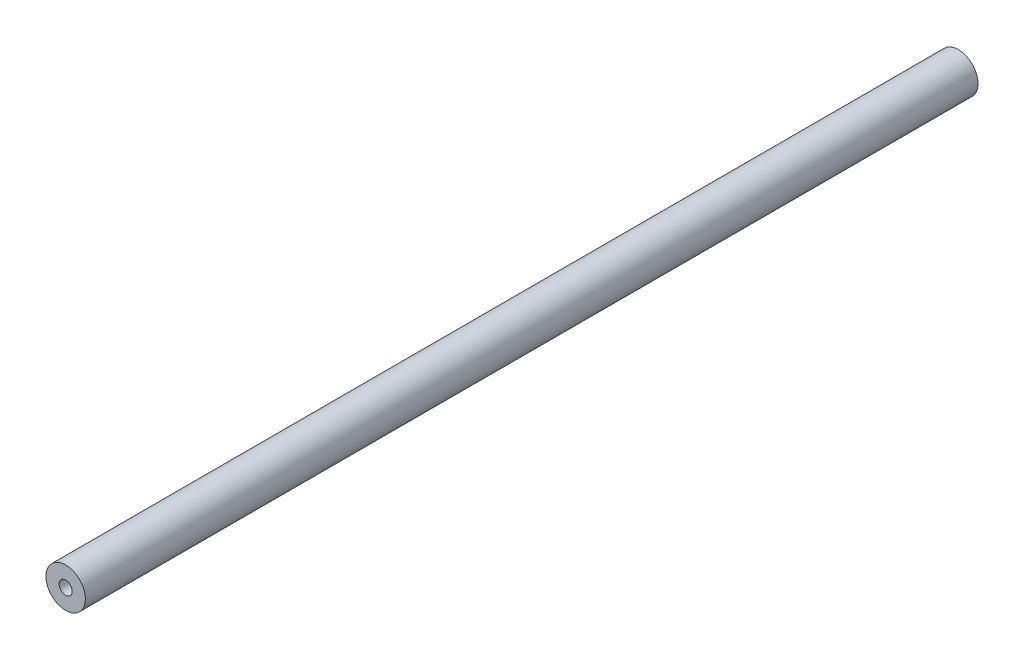
SolidWorks part; units mm, degrees
ref_plane "Front Plane" through (0, 0, 0) normal (0, 0, 1) x (1, 0, 0)
ref_plane "Top Plane" through (0, 0, 0) normal (0, 1, 0) x (1, 0, 0)
ref_plane "Right Plane" through (0, 0, 0) normal (1, 0, 0) x (0, 0, -1)
sketch "Sketch1" plane through (0, 0, 0) normal (0, 0, 1) x (1, 0, 0)
  circle A0 centre (0, 0) radius 4.7625
  circle A1 centre (0, 0) radius 1.5875
  dimension "D1" = 9.525
  dimension "D2" = 3.175
extrude "Boss-Extrude1" add sketch "Sketch1" along normal blind 215.9
